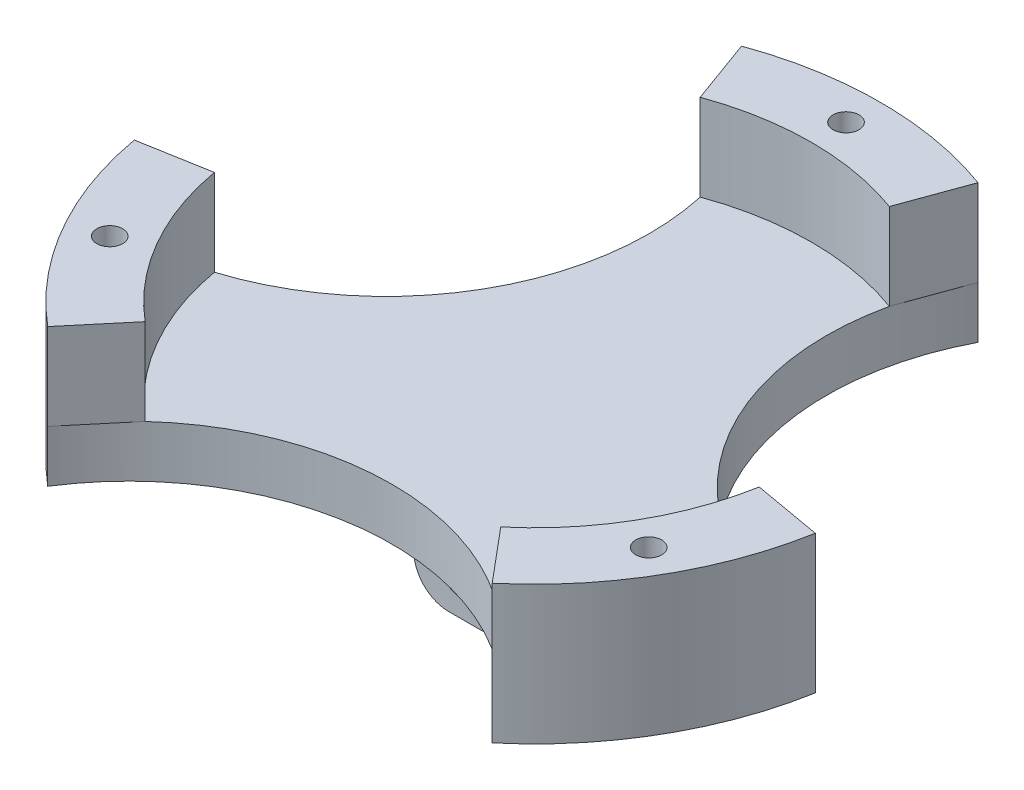
SolidWorks part; units mm, degrees
ref_plane "Front Plane" through (0, 0, 0) normal (0, 0, 1) x (1, 0, 0)
ref_plane "Top Plane" through (0, 0, 0) normal (0, 1, 0) x (1, 0, 0)
ref_plane "Right Plane" through (0, 0, 0) normal (1, 0, 0) x (0, 0, -1)
sketch "Sketch1" plane through (0, 0, 0) normal (0, 1, 0) x (1, 0, 0)
  circle A0 centre (0, 0) radius 40
  dimension "D1" = 80
extrude "Boss-Extrude1" add sketch "Sketch1" along normal blind 6
sketch "Sketch2" plane through (0, 6, 0) normal (0, 1, 0) x (1, 0, 0)
  line L0 (-13.6808, 37.5877) -> (0, 0) construction
  line L1 (0, 0) -> (13.6808, 37.5877) construction
  line L2 (0, -1000) -> (0, 49000) construction
  line L3 (-13.6808, 37.5877) -> (-10.9446, 30.0702)
  line L4 (10.9446, 30.0702) -> (13.6808, 37.5877)
  arc A0 (13.6808, 37.5877) -> (-13.6808, 37.5877) centre (0, 0) ccw
  circle A1 centre (0, 0) radius 40 construction
  arc A2 (10.9446, 30.0702) -> (-10.9446, 30.0702) centre (0, 0) ccw
  circle A3 centre (0, 36) radius 1.5
  dimension "D1" = 8
  dimension "D5" = 3
  dimension "D2" = 20
  dimension "D3" = 20
  dimension "D4" = 36
extrude "Boss-Extrude2" add sketch "Sketch2" along normal blind 10
sketch "Sketch16" plane through (0, 16, 0) normal (0, 1, 0) x (1, 0, 0)
  circle A0 centre (0, 36) radius 1.5
  circle A1 centre (0, 36) radius 1.5 construction
extrude "Cut-Extrude9" cut sketch "Sketch16" against normal through all
pattern_circular "CirPattern1" count 3 over 360 about axis through (0, 0, 0) along (0, 1, 0) of "Boss-Extrude2", "Cut-Extrude9"
sketch "Sketch5" plane through (0, 6, 0) normal (0, 1, 0) x (1, 0, 0)
  circle A1 centre (40.6986, 23.4973) radius 30.4713
extrude "Cut-Extrude3" cut sketch "Sketch5" against normal through all
pattern_circular "CirPattern2" count 3 over 360 about axis through (0, 0, 0) along (0, 1, 0) of "Cut-Extrude3"
sketch "Sketch17" plane through (0, 0, 0) normal (0, -1, 0) x (1, 0, 0)
  line L1 (6, -8) -> (-6, -8)
  line L2 (6, -8) -> (6, 8)
  line L3 (6, 8) -> (-6, 8)
  line L4 (-6, -8) -> (-6, 8)
  line L5 (6, -8) -> (-6, 8) construction
  line L6 (6, 8) -> (-6, -8) construction
  point P0 (0, 0)
  dimension "D1" = 12
  dimension "D2" = 16
extrude "Boss-Extrude3" add sketch "Sketch17" along normal blind 12
fillet "Fillet1" radius 4 4 edges at (6, -12, 0) (6, 0, 0) (-6, -12, 0) (-6, 0, 0)
fillet "Fillet2" radius 4 2 edges at (0, 0, 8) (0, 0, -8)
sketch "Sketch18" plane through (0, 0, 8) normal (0, 0, 1) x (1, 0, 0)
  line L0 (2, -12) -> (-2, -12) construction
  circle A0 centre (0, -6) radius 4
  point P3 (0, 0)
  point P5 (0, -6.233)
  dimension "D1" = 8
  dimension "D2" = 6
extrude "Cut-Extrude10" cut sketch "Sketch18" against normal through all and the other way through all
